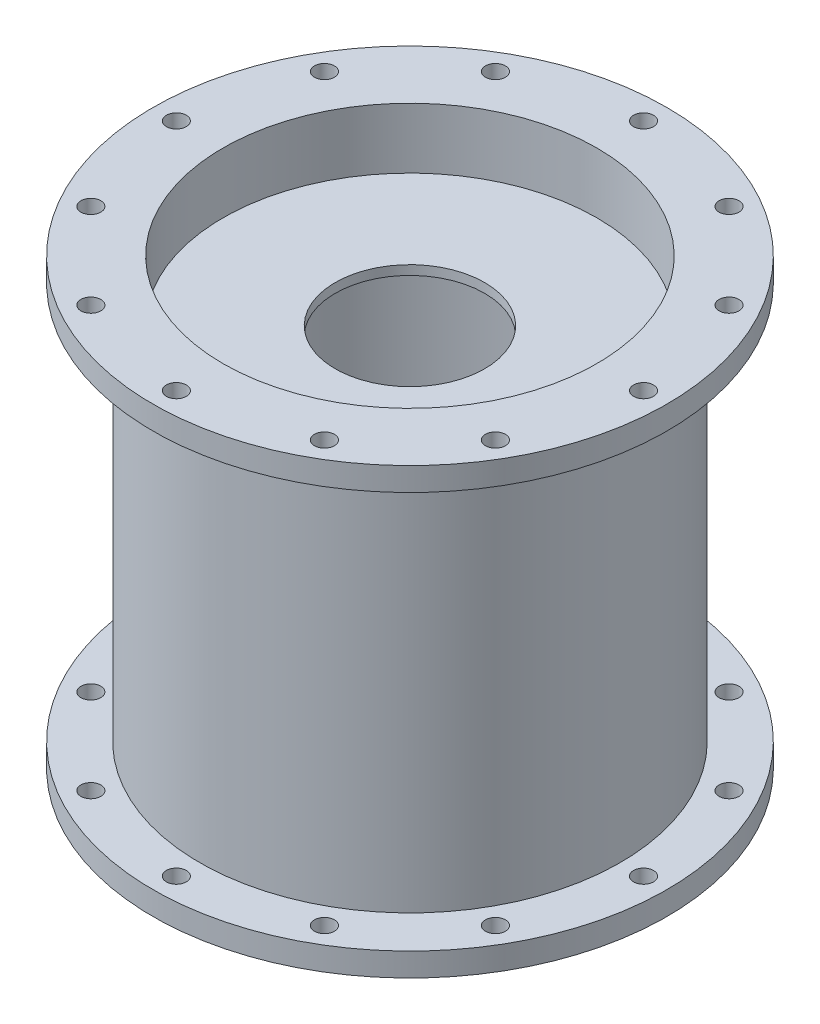
SolidWorks part; units mm, degrees
ref_plane "Front Plane" through (0, 0, 0) normal (0, 0, 1) x (1, 0, 0)
ref_plane "Top Plane" through (0, 0, 0) normal (0, 1, 0) x (1, 0, 0)
ref_plane "Right Plane" through (0, 0, 0) normal (1, 0, 0) x (0, 0, -1)
sketch "Sketch1" plane through (0, 0, 0) normal (1, 0, 0) x (0, 0, -1)
  line L1 (57.15, 6.35) -> (57.15, 114.3)
  line L8 (57.15, 120.65) -> (69.85, 120.65)
  line L9 (69.85, 120.65) -> (69.85, 114.3)
  line L10 (69.85, 114.3) -> (57.15, 114.3)
  line L11 (57.15, 0) -> (69.85, 0)
  line L12 (69.85, 0) -> (69.85, 6.35)
  line L13 (69.85, 6.35) -> (57.15, 6.35)
  line L27 (50.8, 114.3) -> (50.8, 120.65)
  line L28 (50.8, 120.65) -> (57.15, 120.65)
  line L29 (50.8, 6.35) -> (50.8, 0)
  line L30 (50.8, 0) -> (57.15, 0)
  line L31 (50.8, 114.3) -> (50.8, 6.35)
  line L32 (50.8, 0) -> (0, 0) construction
  line L33 (0, 0) -> (0, 6.35) construction
  dimension "D1" = 6.35
  dimension "D2" = 6.35
  dimension "D3" = 12.7
  dimension "D4" = 12.7
  dimension "D5" = 12.7
  dimension "D6" = 12.7
  dimension "D7" = 107.95
  dimension "D8" = 50.8
  dimension "D9" = 6.35
revolve "Chamber" add sketch "Sketch1" angle 360 about L33
sketch "Sketch4" plane through (0, 0, 0) normal (1, 0, 0) x (0, 0, -1)
  line L0 (0, 0) -> (0, 120.65) construction
  line L1 (50.8, 120.65) -> (-50.8, 120.65) construction
  line L3 (50.8, 104.2017) -> (20.32, 104.2017)
  line L7 (50.8, 104.2017) -> (50.8, 101.6617)
  line L8 (0, 60.325) -> (57.15, 60.325) construction
  line L9 (20.32, 104.2017) -> (20.32, 101.6617)
  line L10 (50.8, 16.4483) -> (20.32, 16.4483)
  line L11 (50.8, 16.4483) -> (50.8, 18.9883)
  line L12 (50.8, 18.9883) -> (20.32, 18.9883)
  line L13 (20.32, 16.4483) -> (20.32, 18.9883)
  line L14 (50.8, 101.6617) -> (20.32, 101.6617)
  point P9 (50.7813, 15.9134)
  point P10 (50.342, 18.9883)
  dimension "D1" = 2.54
  dimension "D2" = 30.48
revolve "Turbulence Rings" add sketch "Sketch4" angle 360 about L0
sketch "Sketch5" plane through (0, 120.65, 0) normal (0, 1, 0) x (1, 0, 0)
  line L0 (0, 0) -> (-63.5, 0) construction
  line L1 (0, 0) -> (-54.9926, 31.75) construction
  circle A0 centre (0, 0) radius 63.5 construction
  point P0 (0, 0)
  point P5 (-63.5, 0)
  point P9 (-54.9926, 31.75)
  point P10 (-31.75, 54.9926)
  point P11 (0, 63.5)
  point P12 (31.75, 54.9926)
  point P13 (54.9926, 31.75)
  point P14 (63.5, 0)
  point P15 (54.9926, -31.75)
  point P16 (31.75, -54.9926)
  point P17 (0, -63.5)
  point P18 (-31.75, -54.9926)
  point P19 (-54.9926, -31.75)
  point P20 (0, 0)
  dimension "D1" = 30
  dimension "D2" = 12
hole_wizard "#3 (0.213) Diameter Hole2" positions "Sketch5" profile "Sketch7" hole size "#3" standard "ANSI Inch" end condition through all
sketch "Sketch7" plane through (0, 120.65, 0) normal (1, 0, 0) x (0, 0, 1)
  line L0 (0, 0) -> (0, 120.65)
  line L1 (0, 120.65) -> (2.7051, 120.65)
  line L2 (2.7051, 120.65) -> (2.7051, 0)
  line L5 (2.7051, 0) -> (0, 0)
  line L11 (0, -6.35) -> (0, 107.95) construction
  dimension "Thru Hole Dia." = 5.4102
  dimension "Thru Hole Depth" = 120.65
equation "\"Thickness of Material\"= 0.3in"
equation "\"Chamber Length\"= 4.25in"
equation "\"Flange Length\"= 0.5in"
equation "\"Chamber Wall Thickness\"= 0.25in"
equation "\"Ring Length\"= 1.2in"
equation "\"Ring Thickness\"= 0.1in"
equation "\"Number of Rings\" = 2"
equation "\"Chamber Radius\"= 2in"
